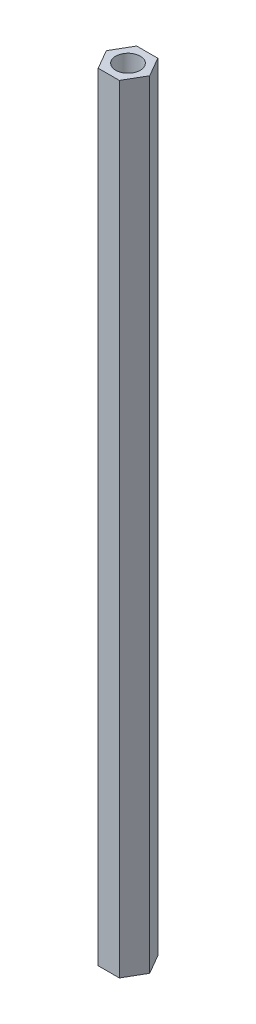
SolidWorks part; units mm, degrees
ref_plane "前视基准面" through (0, 0, 0) normal (0, 0, 1) x (1, 0, 0)
ref_plane "上视基准面" through (0, 0, 0) normal (0, 1, 0) x (1, 0, 0)
ref_plane "右视基准面" through (0, 0, 0) normal (1, 0, 0) x (0, 0, -1)
sketch "草图1" plane through (0, 0, 0) normal (0, 1, 0) x (1, 0, 0)
  line L0 (-12.6472, 0) -> (11.4268, 0) construction
  line L1 (0, 12.1757) -> (0, -13.2296) construction
  line L2 (1.2932, 2.35) -> (-1.2932, 2.35)
  line L7 (1.2932, -2.35) -> (-1.2932, -2.35)
  line L8 (1.2932, 2.35) -> (2.65, 0)
  line L9 (-1.2932, 2.35) -> (-2.65, 0)
  line L10 (1.2932, -2.35) -> (2.65, 0)
  line L11 (-1.2932, -2.35) -> (-2.65, 0)
  circle A0 centre (0, 0) radius 1.5
  point P12 (0, 2.35)
  dimension "D1" = 3
  dimension "D2" = 5.3
  dimension "D3" = 4.7
  dimension "D4" = 120
extrude "凸台-拉伸1" add sketch "草图1" along normal blind 95
